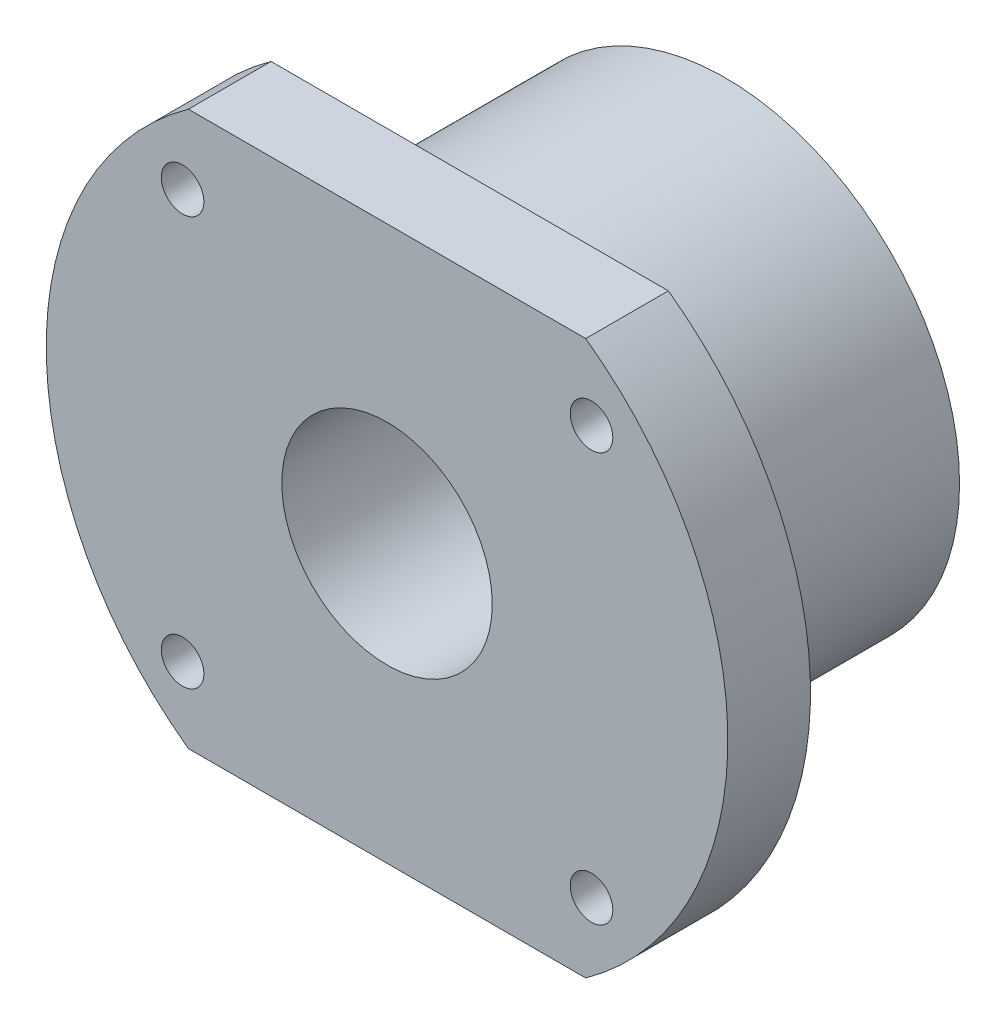
SolidWorks part; units mm, degrees
ref_plane "Płaszczyzna przednia" through (0, 0, 0) normal (0, 0, 1) x (1, 0, 0)
ref_plane "Płaszczyzna górna" through (0, 0, 0) normal (0, 1, 0) x (1, 0, 0)
ref_plane "Płaszczyzna prawa" through (0, 0, 0) normal (1, 0, 0) x (0, 0, -1)
sketch "Szkic1" plane through (0, 0, 0) normal (0, 0, 1) x (1, 0, 0)
  circle A0 centre (0, 0) radius 27.5
extrude "Dodanie-wyciągnięcie1" add sketch "Szkic1" along normal blind 30
sketch "Szkic2" plane through (0, 0, 30) normal (0, 0, 1) x (1, 0, 0)
  circle A0 centre (0, 0) radius 40
extrude "Dodanie-wyciągnięcie2" add sketch "Szkic2" along normal blind 9.7
sketch "Szkic3" plane through (0, 0, 39.7) normal (0, 0, 1) x (1, 0, 0)
  line L0 (-55.0137, 40) -> (-55.0137, 32.5)
  line L1 (-55.0137, 32.5) -> (53.7701, 32.5)
  line L2 (53.7701, 32.5) -> (53.7701, 40)
  line L3 (53.7701, 40) -> (-55.0137, 40)
  circle A0 centre (0, 0) radius 40 construction
  dimension "D1" = 7.5
extrude "Wytnij-wyciągnięcie1" cut sketch "Szkic3" against normal blind 9.7
sketch "Szkic5" plane through (0, 0, 39.7) normal (0, 0, 1) x (1, 0, 0)
  line L0 (-57.8011, -32.5) -> (-57.8011, -40)
  line L1 (-57.8011, -40) -> (50.9828, -40)
  line L2 (50.9828, -40) -> (50.9828, -32.5)
  line L3 (50.9828, -32.5) -> (-57.8011, -32.5)
  circle A1 centre (0, 0) radius 40 construction
  dimension "D1" = 7.5
extrude "Wytnij-wyciągnięcie2" cut sketch "Szkic5" against normal blind 9.7
sketch "Szkic6" plane through (0, 0, 0) normal (0, 0, 1) x (1, 0, 0)
  circle A0 centre (0, 0) radius 12.35
extrude "Wytnij-wyciągnięcie3" cut sketch "Szkic6" along normal blind 39.7
sketch "Szkic7" plane through (0, 0, 39.7) normal (0, 0, 1) x (1, 0, 0)
  circle A0 centre (-24, 24) radius 2.5
  circle A1 centre (24, 24) radius 2.5
  circle A2 centre (-24, -24) radius 2.5
  circle A3 centre (24, -24) radius 2.5
  dimension "D1" = 48
  dimension "D2" = 48
  dimension "D3" = 24
  dimension "D4" = 24
  dimension "D5" = 24
  dimension "D6" = 24
extrude "Wytnij-wyciągnięcie4" cut sketch "Szkic7" against normal blind 9.7
